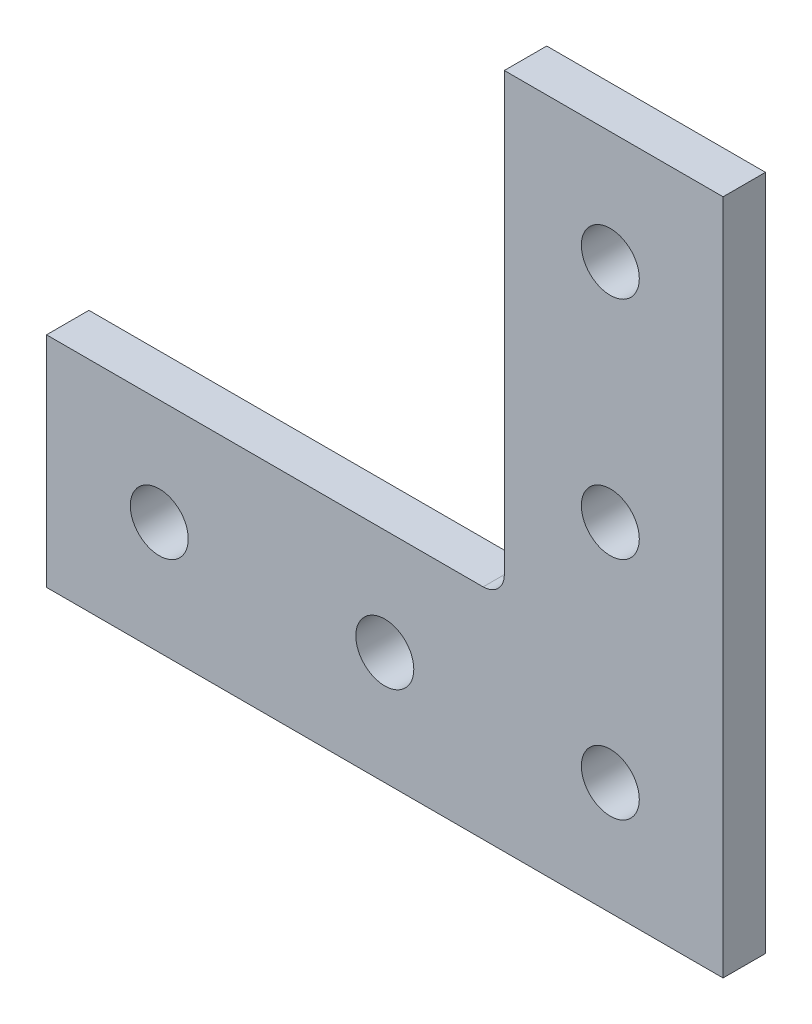
SolidWorks part; units mm, degrees
ref_plane "Front Plane" through (0, 0, 0) normal (0, 0, 1) x (1, 0, 0)
ref_plane "Top Plane" through (0, 0, 0) normal (0, 1, 0) x (1, 0, 0)
ref_plane "Right Plane" through (0, 0, 0) normal (1, 0, 0) x (0, 0, -1)
ref_plane "Plane1" through (0, 0, 0) normal (0, 0, 1) x (1, 0, 0)
sketch "Sketch1" plane through (0, 0, 0) normal (0, 0, 1) x (1, 0, 0)
  line L0 (-76.2, 0) -> (0, 0)
  line L1 (0, 0) -> (0, 76.2)
  line L2 (0, 76.2) -> (-24.638, 76.2)
  line L3 (-24.638, 76.2) -> (-24.638, 27.0256)
  line L4 (-27.0256, 24.638) -> (-76.2, 24.638)
  line L5 (-76.2, 24.638) -> (-76.2, 0)
  arc A0 (-24.638, 27.0256) -> (-27.0256, 24.638) centre (-27.0256, 27.0256) cw
  circle A1 centre (-12.7, 38.1) radius 3.2639
  circle A2 centre (-12.7, 63.5) radius 3.2639
  circle A3 centre (-12.7, 12.7) radius 3.2639
  circle A4 centre (-38.1, 12.7) radius 3.2639
  circle A5 centre (-63.5, 12.7) radius 3.2639
extrude "Boss-Extrude1" add sketch "Sketch1" along normal blind 4.7752
